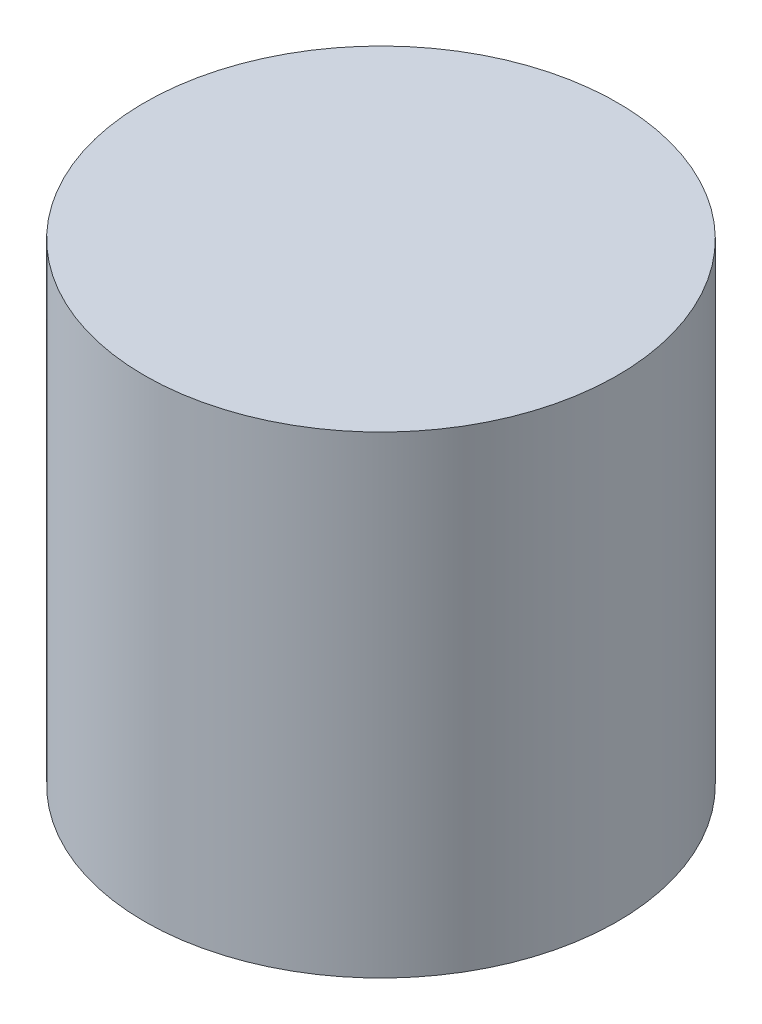
SolidWorks part; units mm, degrees
ref_plane "Front Plane" through (0, 0, 0) normal (0, 0, 1) x (1, 0, 0)
ref_plane "Top Plane" through (0, 0, 0) normal (0, 1, 0) x (1, 0, 0)
ref_plane "Right Plane" through (0, 0, 0) normal (1, 0, 0) x (0, 0, -1)
sketch "Sketch1" plane through (0, 0, 0) normal (0, 1, 0) x (1, 0, 0)
  circle A0 centre (0, 0) radius 12.7
  dimension "D1" = 25.4
extrude "Boss-Extrude1" add sketch "Sketch1" along normal mid plane 25.4
